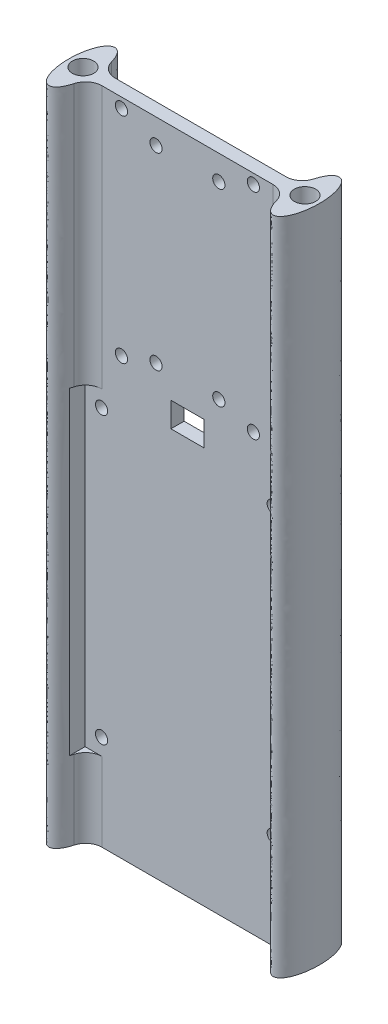
SolidWorks part; units mm, degrees
ref_plane "Front Plane" through (0, 0, 0) normal (0, 0, 1) x (1, 0, 0)
ref_plane "Top Plane" through (0, 0, 0) normal (0, 1, 0) x (1, 0, 0)
ref_plane "Right Plane" through (0, 0, 0) normal (1, 0, 0) x (0, 0, -1)
sketch "Sketch1" plane through (0, 0, 0) normal (0, 1, 0) x (1, 0, 0)
  line L0 (0, 0) -> (0, -2) construction
  line L1 (34, 2) -> (-34, 2)
  line L2 (34, 2) -> (34, -2)
  line L3 (34, -2) -> (-34, -2)
  line L4 (-34, 2) -> (-34, -2)
  line L5 (34, 2) -> (-34, -2) construction
  line L6 (34, -2) -> (-34, 2) construction
  circle A2 centre (-33.655, 0) radius 3.2385
  circle A3 centre (33.655, 0) radius 3.2385
  ellipse E0 centre (-34, 0) end of major axis (-34, -10) minor radius 4
  ellipse E1 centre (34, 0) end of major axis (34, -10) minor radius 4
  point P0 (0, 0)
  dimension "D5" = 6.477
  dimension "D1" = 76
  dimension "D2" = 8
  dimension "D3" = 4
  dimension "D4" = 20
  dimension "D6" = 67.31
extrude "Boss-Extrude1" add sketch "Sketch1" along normal blind 200
fillet "Fillet1" radius 5 4 edges at (30.0808, 100, -2) (30.0808, 100, 2) (-30.0808, 100, -2) (-30.0808, 100, 2)
sketch "Sketch2" plane through (0, 0, 2) normal (0, 0, 1) x (1, 0, 0)
  line L0 (25.8853, 200) -> (-25.8853, 200) construction
  line L1 (-9.525, 192.5) -> (9.525, 192.5)
  line L2 (-9.525, 192.5) -> (-9.525, 135.35)
  line L3 (-9.525, 135.35) -> (9.525, 135.35)
  line L4 (9.525, 192.5) -> (9.525, 135.35)
  line L5 (-9.525, 192.5) -> (9.525, 135.35) construction
  line L6 (-9.525, 135.35) -> (9.525, 192.5) construction
  line L7 (0, 163.925) -> (0, 200) construction
  line L8 (0, 124.1) -> (0, 135.35) construction
  line L9 (5, 127.85) -> (-5, 127.85)
  line L10 (5, 127.85) -> (5, 120.35)
  line L11 (5, 120.35) -> (-5, 120.35)
  line L12 (-5, 127.85) -> (-5, 120.35)
  line L13 (5, 127.85) -> (-5, 120.35) construction
  line L14 (5, 120.35) -> (-5, 127.85) construction
  line L15 (0, 72.1) -> (0, 0) construction
  line L16 (26.03, 28.85) -> (-26.03, 28.85)
  line L17 (26.03, 28.85) -> (26.03, 115.35)
  line L18 (26.03, 115.35) -> (-26.03, 115.35)
  line L19 (-26.03, 28.85) -> (-26.03, 115.35)
  line L20 (26.03, 28.85) -> (-26.03, 115.35) construction
  line L21 (26.03, 115.35) -> (-26.03, 28.85) construction
  circle A0 centre (-9.525, 192.5) radius 1.85
  circle A1 centre (9.525, 192.5) radius 1.85
  circle A2 centre (-9.525, 135.35) radius 1.85
  circle A3 centre (9.525, 135.35) radius 1.85
  circle A4 centre (26.03, 115.35) radius 1.85
  circle A5 centre (-26.03, 115.35) radius 1.85
  circle A6 centre (-26.03, 28.85) radius 1.85
  circle A7 centre (26.03, 28.85) radius 1.85
  point P0 (0, 163.925)
  point P9 (0, 124.1)
  point P16 (0, 72.1)
  point P24 (0, 115.35)
  line M11 (25.8853, 0) -> (25.8853, 200)
  line M13 (-25.8853, 200) -> (-25.8853, 0)
  dimension "D10" = 3.7
  dimension "D1" = 7.5
  dimension "D2" = 19.05
  dimension "D3" = 57.15
  dimension "D4" = 10
  dimension "D5" = 7.5
  dimension "D6" = 7.5
  dimension "D7" = 52.06
  dimension "D8" = 86.5
  dimension "D9" = 5
sketch "Sketch3" plane through (0, 0, -2) normal (0, 0, -1) x (-1, 0, 0)
  line L0 (0, 164.5) -> (0, 0) construction
  line L1 (20, 132) -> (-20, 132)
  line L2 (20, 132) -> (20, 197)
  line L3 (20, 197) -> (-20, 197)
  line L4 (-20, 132) -> (-20, 197)
  line L5 (20, 132) -> (-20, 197) construction
  line L6 (20, 197) -> (-20, 132) construction
  line L7 (-25.8853, 200) -> (25.8853, 200) construction
  circle A0 centre (-20, 197) radius 1.85
  circle A1 centre (20, 197) radius 1.85
  circle A2 centre (20, 132) radius 1.85
  circle A3 centre (-20, 132) radius 1.85
  point P0 (0, 164.5)
  dimension "D4" = 3.7
  dimension "D1" = 40
  dimension "D2" = 65
  dimension "D3" = 3
extrude "Cut-Extrude1" cut sketch "Sketch3" against normal through all both and the other way through all contours L3 A0 L4 | L2 A1 L3 | L3 A1 L2 | L4 A0 L3 | L1 A3 L4 | L4 A3 L1 | L2 A2 L1 | L1 A2 L2
extrude "Cut-Extrude2" cut sketch "Sketch2" against normal through all both and the other way through all contours L19 A6 L16 M13 | A6 L19 L16 M13 | L16 A6 M13 | A6 L16 M13 | L17 A7 L16 M11 | A7 L16 M11 | A7 L17 L16 M11 | L16 A7 M11 | A4 L17 L18 M11 | L18 A4 M11 | A4 L18 M11 | L17 A4 L18 M11 | L19 A5 L18 M13 | A5 L18 M13 | L18 A5 M13 | A5 L19 L18 M13 | L9 L12 L11 L10 | L4 A3 L3 | L3 A3 L4 | L2 A2 L3 | L3 A2 L2 | L2 A0 L1 | L1 A0 L2 | L1 A1 L4 | L4 A1 L1
sketch "Sketch4" plane through (0, 0, 2) normal (0, 0, 1) x (1, 0, 0)
  line L8 (31.03, 23.85) -> (31.03, 120.35)
  line L9 (-31.03, 23.85) -> (31.03, 23.85)
  line L10 (-31.03, 120.35) -> (-31.03, 23.85)
  line L11 (31.03, 120.35) -> (-31.03, 120.35)
  line L12 (31.03, 23.85) -> (31.03, 120.35)
  line L13 (-31.03, 23.85) -> (31.03, 23.85)
  line L14 (-31.03, 120.35) -> (-31.03, 23.85)
  line L15 (31.03, 120.35) -> (-31.03, 120.35)
  dimension "D1" = 5
extrude "Cut-Extrude3" cut sketch "Sketch4" along normal blind 10
